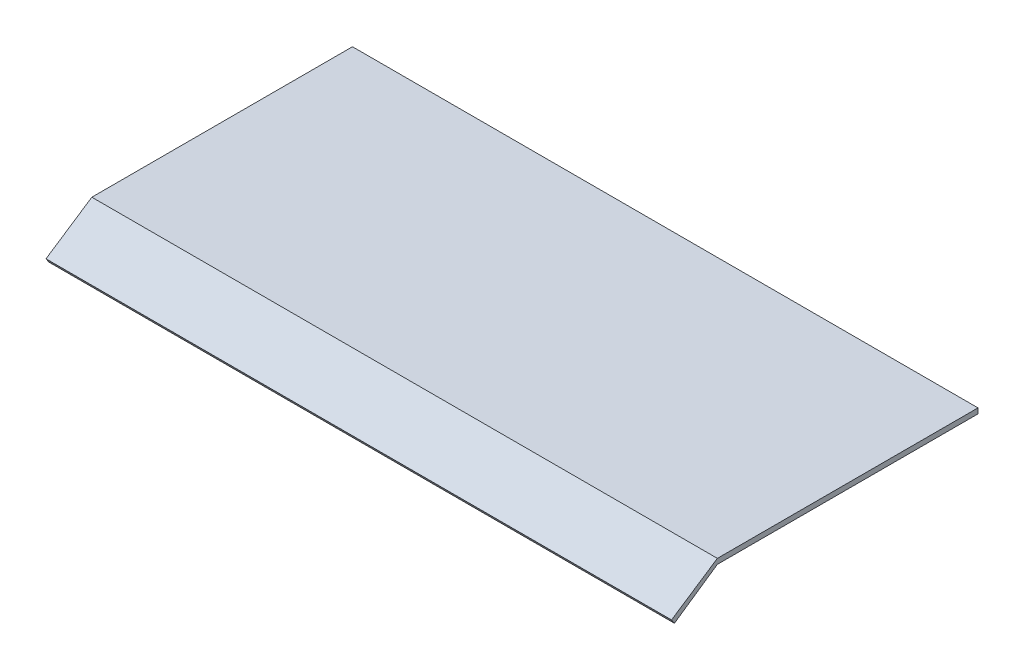
SolidWorks part; units mm, degrees
ref_plane "Front" through (0, 0, 0) normal (0, 0, 1) x (1, 0, 0)
ref_plane "Top" through (0, 0, 0) normal (0, 1, 0) x (1, 0, 0)
ref_plane "Right" through (0, 0, 0) normal (1, 0, 0) x (0, 0, -1)
sketch "Sketch1" plane through (0, 0, 0) normal (1, 0, 0) x (0, 0, -1)
  line L0 (0, 0) -> (127, 0)
  line L1 (127, 0) -> (127, -2.54)
  line L2 (127, -2.54) -> (0, -2.54)
  line L3 (0, -2.54) -> (-20.9282, -16.9334)
  line L6 (-22.3309, -14.8198) -> (0, 0)
  line L7 (-20.9282, -16.9334) -> (-22.3309, -14.8198)
  dimension "D1" = 127
  dimension "D2" = 2.54
  dimension "D3" = 25.4
extrude "Boss-Extrude1" add sketch "Sketch1" along normal blind 304.8
